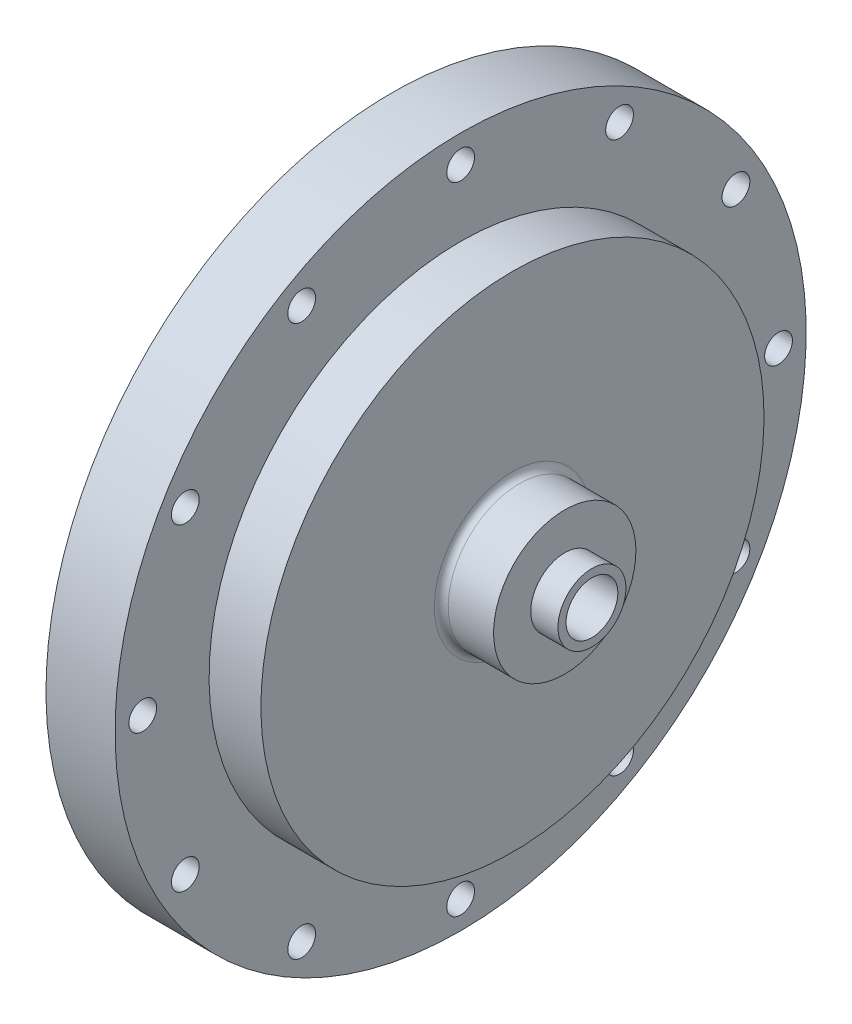
SolidWorks part; units mm, degrees
material "7075-T6 (SN)"
ref_plane "Front Plane" through (0, 0, 0) normal (0, 0, 1) x (1, 0, 0)
ref_plane "Top Plane" through (0, 0, 0) normal (0, 1, 0) x (1, 0, 0)
ref_plane "Right Plane" through (0, 0, 0) normal (1, 0, 0) x (0, 0, -1)
sketch "Sketch2" plane through (0, 0, 0) normal (0, 0, 1) x (1, 0, 0)
  line L0 (9.525, 0) -> (165.0115, 0) construction
  line L5 (41.355, 13.081) -> (41.355, 6.2484)
  line L6 (31.75, 13.081) -> (41.355, 13.081)
  line L7 (41.355, 6.2484) -> (46.355, 6.2484)
  line L8 (46.355, 6.2484) -> (46.355, 0)
  line L9 (9.525, 0) -> (46.355, 0)
  line L16 (9.525, 0) -> (9.525, 63.5)
  line L18 (31.75, 63.5) -> (31.75, 13.081)
  line L19 (31.75, 63.5) -> (9.525, 63.5)
  dimension "D1" = 63.5
  dimension "D2" = 36.83
  dimension "D4" = 13.081
  dimension "D5" = 22.225
  dimension "D7" = 6.2484
  dimension "D8" = 5
revolve "Main Structure" add sketch "Sketch2" angle 360 about L0
cosmetic thread "Cosmetic Thread1" parameters "D2"=23.1953
sketch "Sketch3" plane through (46.355, 0, 0) normal (1, 0, 0) x (0, 0, -1)
  circle A0 centre (0, 0) radius 4.7625
  dimension "D1" = 9.525
extrude "Oxidizer Inlet Hole" cut sketch "Sketch3" against normal through all
sketch "Sketch4" plane through (31.75, 0, 0) normal (-1, 0, 0) x (0, 0, 1)
  circle A0 centre (0, 0) radius 58.42 construction
  circle A1 centre (0, -58.42) radius 2.146
  circle A2 centre (-29.21, -50.5932) radius 2.146
  circle A3 centre (-50.5932, -29.21) radius 2.146
  circle A4 centre (-58.42, 0) radius 2.146
  circle A5 centre (-50.5932, 29.21) radius 2.146
  circle A6 centre (-29.21, 50.5932) radius 2.146
  circle A7 centre (0, 58.42) radius 2.146
  circle A8 centre (29.21, 50.5932) radius 2.146
  circle A9 centre (50.5932, 29.21) radius 2.146
  circle A10 centre (58.42, 0) radius 2.146
  circle A11 centre (50.5932, -29.21) radius 2.146
  circle A12 centre (29.21, -50.5932) radius 2.146
  point P29 (0, 0)
  dimension "D1" = 12
  dimension "D2" = 116.84
hole_wizard "Flange Holes" positions "Sketch7" profile "Sketch8" hole size "#7" standard "ANSI Inch" end condition up to next
sketch "Sketch7" plane through (31.75, 0, 0) normal (-1, 0, 0) x (0, 0, 1)
  point P0 (0, -58.42)
  point P3 (-29.21, -50.5932)
  point P6 (-50.5932, -29.21)
  point P9 (-58.42, 0)
  point P12 (-50.5932, 29.21)
  point P15 (-29.21, 50.5932)
  point P18 (0, 58.42)
  point P21 (29.21, 50.5932)
  point P24 (50.5932, 29.21)
  point P27 (58.42, 0)
  point P30 (50.5932, -29.21)
  point P33 (29.21, -50.5932)
sketch "Sketch8" plane through (31.75, -58.42, 0) normal (0, 1, 0) x (0, 0, -1)
  line L0 (0, 0) -> (0, 22.225)
  line L1 (0, 22.225) -> (2.5527, 22.225)
  line L2 (2.5527, 22.225) -> (2.5527, 0)
  line L5 (2.5527, 0) -> (0, 0)
  line L11 (0, -6.35) -> (0, 107.95) construction
  dimension "Thru Hole Dia." = 5.1054
  dimension "Thru Hole Depth" = 22.225
sketch "Sketch9" plane through (9.525, 0, 0) normal (-1, 0, 0) x (0, 0, 1)
  line L0 (0, 0) -> (-67.6727, 18.1329) construction
  line L1 (0, 0) -> (-58.42, 0) construction
  circle A0 centre (0, 0) radius 58.42 construction
  circle A1 centre (-56.4294, 15.1202) radius 2.9451
  circle A2 centre (56.4294, -15.1202) radius 2.9451
  point P14 (0, 0)
  dimension "D1" = 15
  dimension "D2" = 2
hole_wizard "Dowel Holes" positions "Sketch10" profile "Sketch11" hole size "3/16" standard "ANSI Inch"
sketch "Sketch10" plane through (9.525, 0, 0) normal (-1, 0, 0) x (0, 0, 1)
  point P0 (56.4294, -15.1202)
  point P3 (-56.4294, 15.1202)
sketch "Sketch11" plane through (9.525, -15.1202, 56.4294) normal (0, 1, 0) x (0, 0, 1)
  line L0 (0, 0) -> (0, 7.7808)
  line L1 (0, 7.7808) -> (2.3812, 6.35)
  line L2 (2.3812, 6.35) -> (2.3812, 0)
  line L5 (2.3812, 0) -> (0, 0)
  line L10 (0, 7.7808) -> (-2.3812, 6.35) construction
  line L11 (0, -6.35) -> (0, 107.95) construction
  dimension "Hole Dia." = 4.7625
  dimension "Hole Depth" = 6.35
  dimension "Drill Angle" = 118
sketch "Sketch12" plane through (9.525, 0, 0) normal (-1, 0, 0) x (0, 0, 1)
  circle A0 centre (0, 0) radius 28.575
  dimension "D1" = 57.15
extrude "Cut-Extrude2" cut sketch "Sketch12" against normal blind 9.525
ref_plane "Plane1" through (9.525, 0, 0) normal (-1, 0, 0) x (0, 0, 1)
ref_plane "Plane4" through (19.05, 0, 0) normal (-1, 0, 0) x (0, 0, 1)
sketch "Sketch16" plane through (19.05, 0, 0) normal (-1, 0, 0) x (0, 0, 1)
  circle A0 centre (0, 0) radius 28.575
  dimension "D1" = 57.15
ref_plane "Plane2" through (30.48, 0, 0) normal (-1, 0, 0) x (0, 0, 1)
sketch "Sketch17" plane through (30.48, 0, 0) normal (-1, 0, 0) x (0, 0, 1)
  circle A0 centre (0, 0) radius 4.7625
  dimension "D1" = 9.525
loft "Internal Flow Path Loft Cut" cut profiles "Sketch16", "Sketch17"
sketch "Sketch18" plane through (9.525, 0, 0) normal (-1, 0, 0) x (0, 0, 1)
  circle A0 centre (0, 0) radius 33.3375
  circle A1 centre (33.3375, 0) radius 1.5042
  dimension "D1" = 66.675
hole_wizard "#4-40 Tapped Hole1" positions "Sketch19" profile "Sketch20" tap size "#4-40" standard "ANSI Inch"
sketch "Sketch19" plane through (9.525, 0, 0) normal (-1, 0, 0) x (0, 0, 1)
  point P0 (33.3375, 0)
sketch "Sketch20" plane through (9.525, 0, 33.3375) normal (0, 1, 0) x (0, 0, 1)
  line L0 (0, 0) -> (0, 13.8872)
  line L1 (0, 13.8872) -> (1.1303, 13.208)
  line L2 (1.1303, 13.208) -> (1.1303, 0)
  line L5 (1.1303, 0) -> (0, 0)
  line L10 (0, 13.8872) -> (-1.1303, 13.208) construction
  line L11 (0, -6.35) -> (0, 107.95) construction
  dimension "Tap Drill Dia." = 2.2606
  dimension "Tap Drill Depth" = 13.208
  dimension "Drill Angle" = 118
cosmetic thread "Hole Thread1" parameters "D1"=9.398, "D2"=2.8448
pattern_circular "CirPattern1" count 8 over 360 about axis through (0, 0, 0) along (1, 0, 0) of "#4-40 Tapped Hole1"
fillet "Fillet1" radius 1.27 1 edges at (31.75, -13.081, 0)
sketch "Sketch23" plane through (9.525, 0, 0) normal (-1, 0, 0) x (0, 0, 1)
  circle A0 centre (0, 0) radius 44.45
  circle A1 centre (0, 0) radius 63.5
  dimension "D1" = 88.9
split line "Split Line5"
sketch "Sketch25" plane through (31.75, 0, 0) normal (1, 0, 0) x (0, 0, -1)
  circle A0 centre (0, 0) radius 46.228
  dimension "D1" = 92.456
extrude "Cut-Extrude3" cut sketch "Sketch25" against normal blind 9.525 flip side to cut
